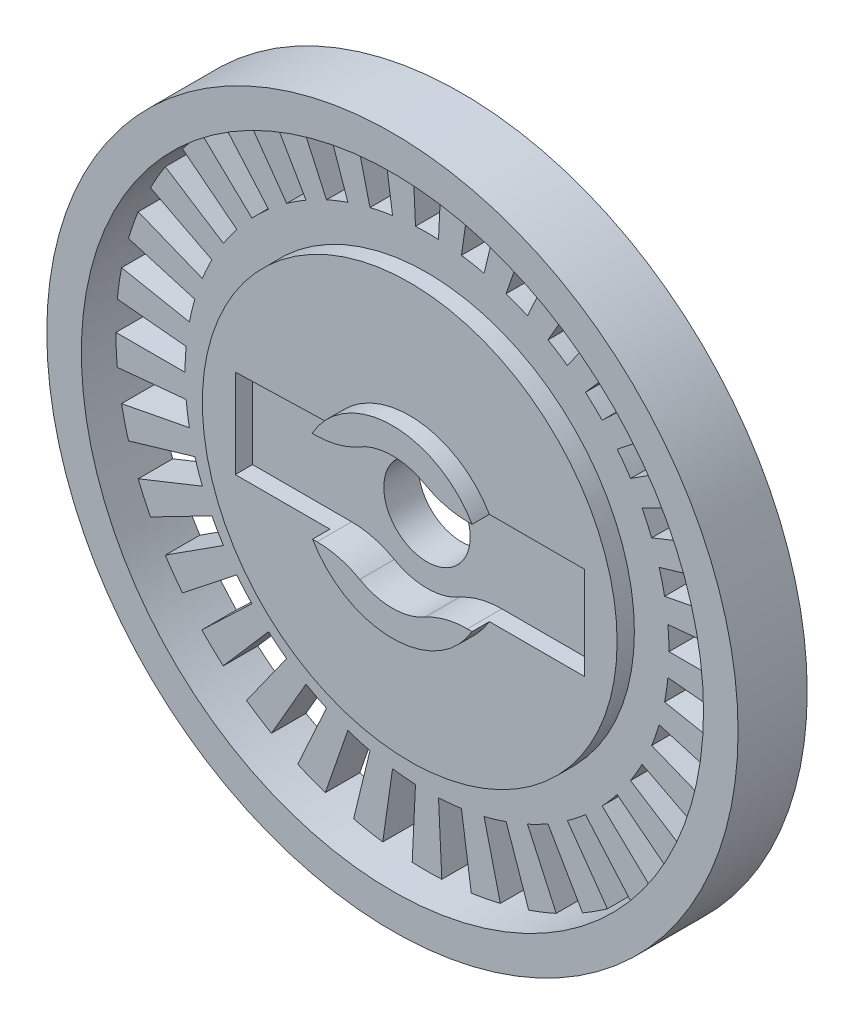
SolidWorks part; units mm, degrees
material "ABS"
ref_plane "Front Plane" through (0, 0, 0) normal (0, 0, 1) x (1, 0, 0)
ref_plane "Top Plane" through (0, 0, 0) normal (0, 1, 0) x (1, 0, 0)
ref_plane "Right Plane" through (0, 0, 0) normal (1, 0, 0) x (0, 0, -1)
sketch "Sketch1" plane through (0, 0, 0) normal (0, 0, 1) x (1, 0, 0)
  circle A0 centre (0, 0) radius 20
  dimension "D1" = 40
extrude "Boss-Extrude1" add sketch "Sketch1" along normal blind 4
sketch "Sketch2" plane through (0, 0, 4) normal (0, 0, 1) x (1, 0, 0)
  circle A0 centre (0, 0) radius 2.5
  dimension "D1" = 5
extrude "Cut-Extrude1" cut sketch "Sketch2" against normal blind 4
sketch "Sketch3" plane through (0, 0, 4) normal (0, 0, 1) x (1, 0, 0)
  line L6 (0, 0) -> (10.109, 0.0032) construction
  line L13 (10.075, 1.7016) -> (2.716, 2.6933) construction
  line L14 (10, 1.6361) -> (2.6806, 2.6224) construction
  line L15 (2.7051, -2.5972) -> (10, -5.8129) construction
  line L16 (2.7225, -2.6868) -> (10.075, -5.9279) construction
  line L17 (10.075, -5.9279) -> (10.075, 1.7016) construction
  line L18 (10, -5.8129) -> (10, 1.6361) construction
  line L19 (-10.075, 2.1965) -> (-2.9216, 2.4688) construction
  line L20 (-10, 2.1243) -> (-2.8855, 2.3951) construction
  line L21 (-2.7034, -2.5989) -> (-10, -1.9654) construction
  line L22 (-2.7378, -2.6712) -> (-10.075, -2.0342) construction
  line L23 (-10.075, -2.0342) -> (-10.075, 2.1965) construction
  line L24 (-10, -1.9654) -> (-10, 2.1243) construction
  line L25 (-2.7378, -2.6712) -> (-10.0936, -2.6712)
  line L26 (-10.0936, -2.6712) -> (-10.0936, 2.4688)
  line L29 (10.109, 0.0032) -> (10.109, -2.6868)
  line L30 (10.109, -2.6868) -> (2.7225, -2.6868)
  line L31 (2.7207, 2.6885) -> (10.109, 2.6885)
  line L32 (-2.7395, 2.6694) -> (-10.0936, 2.4688)
  line L33 (10.109, 2.6885) -> (10.109, 0.0032)
  arc A0 (-2.7034, -2.5989) -> (2.7051, -2.5972) centre (0, 0) ccw construction
  arc A1 (-2.7395, 2.6694) -> (2.7207, 2.6885) centre (0, 0) cw
  arc A4 (-2.7378, -2.6712) -> (2.7225, -2.6868) centre (0, 0) ccw
  arc A5 (2.6806, 2.6224) -> (-2.8855, 2.3951) centre (0, 0) ccw construction
  arc A6 (2.716, 2.6933) -> (-2.9216, 2.4688) centre (0, 0) ccw construction
  dimension "D1" = 5.4603
  dimension "D3" = 0.075
extrude "Cut-Extrude2" cut sketch "Sketch3" against normal blind 2
sketch "Sketch4" plane through (0, 0, 4) normal (0, 0, 1) x (1, 0, 0)
  line L0 (0, 0) -> (15, 0) construction
  line L1 (0, 0) -> (14.9321, 1.4258) construction
  line L2 (13.9366, 1.3308) -> (17.9185, 1.711)
  line L3 (14, 0) -> (18, 0)
  line L4 (-20, 0) -> (20, 0) construction
  line L5 (13.9366, -1.3308) -> (17.9185, -1.711)
  line L6 (13.747, -2.6495) -> (17.6747, -3.4065)
  line L7 (13.4329, -3.9443) -> (17.2709, -5.0712)
  line L8 (12.9972, -5.2033) -> (16.7106, -6.6899)
  line L9 (12.4437, -6.4152) -> (15.999, -8.2481)
  line L10 (11.7775, -7.569) -> (15.1426, -9.7315)
  line L11 (11.0047, -8.6542) -> (14.149, -11.1269)
  line L12 (10.1323, -9.6611) -> (13.0272, -12.4214)
  line L13 (9.1681, -10.5805) -> (11.7875, -13.6035)
  line L14 (8.1208, -11.4041) -> (10.441, -14.6624)
  line L15 (7, -12.1244) -> (9, -15.5885)
  line L16 (5.8158, -12.7348) -> (7.4775, -16.3734)
  line L17 (4.579, -13.23) -> (5.8872, -17.01)
  line L18 (3.3006, -13.6054) -> (4.2437, -17.4926)
  line L19 (1.9924, -13.8575) -> (2.5617, -17.8168)
  line L20 (0.6661, -13.9841) -> (0.8565, -17.9796)
  line L21 (-0.6661, -13.9841) -> (-0.8565, -17.9796)
  line L22 (-1.9924, -13.8575) -> (-2.5617, -17.8168)
  line L23 (-3.3006, -13.6054) -> (-4.2437, -17.4926)
  line L24 (-4.579, -13.23) -> (-5.8872, -17.01)
  line L25 (-5.8158, -12.7348) -> (-7.4775, -16.3734)
  line L26 (-7, -12.1244) -> (-9, -15.5885)
  line L27 (-8.1208, -11.4041) -> (-10.441, -14.6624)
  line L28 (-9.1681, -10.5805) -> (-11.7875, -13.6035)
  line L29 (-10.1323, -9.6611) -> (-13.0272, -12.4214)
  line L30 (-11.0047, -8.6542) -> (-14.149, -11.1269)
  line L31 (-11.7775, -7.569) -> (-15.1426, -9.7315)
  line L32 (-12.4437, -6.4152) -> (-15.999, -8.2481)
  line L33 (-12.9972, -5.2033) -> (-16.7106, -6.6899)
  line L34 (-13.4329, -3.9443) -> (-17.2709, -5.0712)
  line L35 (-13.747, -2.6495) -> (-17.6747, -3.4065)
  line L36 (-13.9366, -1.3308) -> (-17.9185, -1.711)
  line L37 (-14, 0) -> (-18, 0)
  line L38 (-13.9366, 1.3308) -> (-17.9185, 1.711)
  line L39 (-13.747, 2.6495) -> (-17.6747, 3.4065)
  line L40 (-13.4329, 3.9443) -> (-17.2709, 5.0712)
  line L41 (-12.9972, 5.2033) -> (-16.7106, 6.6899)
  line L42 (-12.4437, 6.4152) -> (-15.999, 8.2481)
  line L43 (-11.7775, 7.569) -> (-15.1426, 9.7315)
  line L44 (-11.0047, 8.6542) -> (-14.149, 11.1269)
  line L45 (-10.1323, 9.6611) -> (-13.0272, 12.4214)
  line L46 (-9.1681, 10.5805) -> (-11.7875, 13.6035)
  line L47 (-8.1208, 11.4041) -> (-10.441, 14.6624)
  line L48 (-7, 12.1244) -> (-9, 15.5885)
  line L49 (-5.8158, 12.7348) -> (-7.4775, 16.3734)
  line L50 (-4.579, 13.23) -> (-5.8872, 17.01)
  line L51 (-3.3006, 13.6054) -> (-4.2437, 17.4926)
  line L52 (-1.9924, 13.8575) -> (-2.5617, 17.8168)
  line L53 (-0.6661, 13.9841) -> (-0.8565, 17.9796)
  line L54 (0.6661, 13.9841) -> (0.8565, 17.9796)
  line L55 (1.9924, 13.8575) -> (2.5617, 17.8168)
  line L56 (3.3006, 13.6054) -> (4.2437, 17.4926)
  line L57 (4.579, 13.23) -> (5.8872, 17.01)
  line L58 (5.8158, 12.7348) -> (7.4775, 16.3734)
  line L59 (7, 12.1244) -> (9, 15.5885)
  line L60 (8.1208, 11.4041) -> (10.441, 14.6624)
  line L61 (9.1681, 10.5805) -> (11.7875, 13.6035)
  line L62 (10.1323, 9.6611) -> (13.0272, 12.4214)
  line L63 (11.0047, 8.6542) -> (14.149, 11.1269)
  line L64 (11.7775, 7.569) -> (15.1426, 9.7315)
  line L65 (12.4437, 6.4152) -> (15.999, 8.2481)
  line L66 (12.9972, 5.2033) -> (16.7106, 6.6899)
  line L67 (13.4329, 3.9443) -> (17.2709, 5.0712)
  line L68 (13.747, 2.6495) -> (17.6747, 3.4065)
  line L69 (0, 0) -> (19.3185, -5.1764) construction
  line L70 (0, 0) -> (-19.3185, -5.1764) construction
  circle A0 centre (0, 0) radius 15 construction
  arc A1 (14, 0) -> (13.9366, 1.3308) centre (0, 0) ccw construction
  arc A2 (18, 0) -> (17.9185, 1.711) centre (0, 0) ccw
  arc A3 (13.9366, 1.3308) -> (14, 0) centre (0, 0) cw
  circle A4 centre (0, 0) radius 20 construction
  arc A5 (17.6747, -3.4065) -> (17.9185, -1.711) centre (0, 0) ccw
  arc A6 (13.9366, -1.3308) -> (13.747, -2.6495) centre (0, 0) cw
  arc A7 (16.7106, -6.6899) -> (17.2709, -5.0712) centre (0, 0) ccw
  arc A8 (13.4329, -3.9443) -> (12.9972, -5.2033) centre (0, 0) cw
  arc A9 (15.1426, -9.7315) -> (15.999, -8.2481) centre (0, 0) ccw
  arc A10 (12.4437, -6.4152) -> (11.7775, -7.569) centre (0, 0) cw
  arc A11 (13.0272, -12.4214) -> (14.149, -11.1269) centre (0, 0) ccw
  arc A12 (11.0047, -8.6542) -> (10.1323, -9.6611) centre (0, 0) cw
  arc A13 (10.441, -14.6624) -> (11.7875, -13.6035) centre (0, 0) ccw
  arc A14 (9.1681, -10.5805) -> (8.1208, -11.4041) centre (0, 0) cw
  arc A15 (7.4775, -16.3734) -> (9, -15.5885) centre (0, 0) ccw
  arc A16 (7, -12.1244) -> (5.8158, -12.7348) centre (0, 0) cw
  arc A17 (4.2437, -17.4926) -> (5.8872, -17.01) centre (0, 0) ccw
  arc A18 (4.579, -13.23) -> (3.3006, -13.6054) centre (0, 0) cw
  arc A19 (0.8565, -17.9796) -> (2.5617, -17.8168) centre (0, 0) ccw
  arc A20 (1.9924, -13.8575) -> (0.6661, -13.9841) centre (0, 0) cw
  arc A21 (-2.5617, -17.8168) -> (-0.8565, -17.9796) centre (0, 0) ccw
  arc A22 (-0.6661, -13.9841) -> (-1.9924, -13.8575) centre (0, 0) cw
  arc A23 (-5.8872, -17.01) -> (-4.2437, -17.4926) centre (0, 0) ccw
  arc A24 (-3.3006, -13.6054) -> (-4.579, -13.23) centre (0, 0) cw
  arc A25 (-9, -15.5885) -> (-7.4775, -16.3734) centre (0, 0) ccw
  arc A26 (-5.8158, -12.7348) -> (-7, -12.1244) centre (0, 0) cw
  arc A27 (-11.7875, -13.6035) -> (-10.441, -14.6624) centre (0, 0) ccw
  arc A28 (-8.1208, -11.4041) -> (-9.1681, -10.5805) centre (0, 0) cw
  arc A29 (-14.149, -11.1269) -> (-13.0272, -12.4214) centre (0, 0) ccw
  arc A30 (-10.1323, -9.6611) -> (-11.0047, -8.6542) centre (0, 0) cw
  arc A31 (-15.999, -8.2481) -> (-15.1426, -9.7315) centre (0, 0) ccw
  arc A32 (-11.7775, -7.569) -> (-12.4437, -6.4152) centre (0, 0) cw
  arc A33 (-17.2709, -5.0712) -> (-16.7106, -6.6899) centre (0, 0) ccw
  arc A34 (-12.9972, -5.2033) -> (-13.4329, -3.9443) centre (0, 0) cw
  arc A35 (-17.9185, -1.711) -> (-17.6747, -3.4065) centre (0, 0) ccw
  arc A36 (-13.747, -2.6495) -> (-13.9366, -1.3308) centre (0, 0) cw
  arc A37 (-17.9185, 1.711) -> (-18, 0) centre (0, 0) ccw
  arc A38 (-14, 0) -> (-13.9366, 1.3308) centre (0, 0) cw
  arc A39 (-17.2709, 5.0712) -> (-17.6747, 3.4065) centre (0, 0) ccw
  arc A40 (-13.747, 2.6495) -> (-13.4329, 3.9443) centre (0, 0) cw
  arc A41 (-15.999, 8.2481) -> (-16.7106, 6.6899) centre (0, 0) ccw
  arc A42 (-12.9972, 5.2033) -> (-12.4437, 6.4152) centre (0, 0) cw
  arc A43 (-14.149, 11.1269) -> (-15.1426, 9.7315) centre (0, 0) ccw
  arc A44 (-11.7775, 7.569) -> (-11.0047, 8.6542) centre (0, 0) cw
  arc A45 (-11.7875, 13.6035) -> (-13.0272, 12.4214) centre (0, 0) ccw
  arc A46 (-10.1323, 9.6611) -> (-9.1681, 10.5805) centre (0, 0) cw
  arc A47 (-9, 15.5885) -> (-10.441, 14.6624) centre (0, 0) ccw
  arc A48 (-8.1208, 11.4041) -> (-7, 12.1244) centre (0, 0) cw
  arc A49 (-5.8872, 17.01) -> (-7.4775, 16.3734) centre (0, 0) ccw
  arc A50 (-5.8158, 12.7348) -> (-4.579, 13.23) centre (0, 0) cw
  arc A51 (-2.5617, 17.8168) -> (-4.2437, 17.4926) centre (0, 0) ccw
  arc A52 (-3.3006, 13.6054) -> (-1.9924, 13.8575) centre (0, 0) cw
  arc A53 (0.8565, 17.9796) -> (-0.8565, 17.9796) centre (0, 0) ccw
  arc A54 (-0.6661, 13.9841) -> (0.6661, 13.9841) centre (0, 0) cw
  arc A55 (4.2437, 17.4926) -> (2.5617, 17.8168) centre (0, 0) ccw
  arc A56 (1.9924, 13.8575) -> (3.3006, 13.6054) centre (0, 0) cw
  arc A57 (7.4775, 16.3734) -> (5.8872, 17.01) centre (0, 0) ccw
  arc A58 (4.579, 13.23) -> (5.8158, 12.7348) centre (0, 0) cw
  arc A59 (10.441, 14.6624) -> (9, 15.5885) centre (0, 0) ccw
  arc A60 (7, 12.1244) -> (8.1208, 11.4041) centre (0, 0) cw
  arc A61 (13.0272, 12.4214) -> (11.7875, 13.6035) centre (0, 0) ccw
  arc A62 (9.1681, 10.5805) -> (10.1323, 9.6611) centre (0, 0) cw
  arc A63 (15.1426, 9.7315) -> (14.149, 11.1269) centre (0, 0) ccw
  arc A64 (11.0047, 8.6542) -> (11.7775, 7.569) centre (0, 0) cw
  arc A65 (16.7106, 6.6899) -> (15.999, 8.2481) centre (0, 0) ccw
  arc A66 (12.4437, 6.4152) -> (12.9972, 5.2033) centre (0, 0) cw
  arc A67 (17.6747, 3.4065) -> (17.2709, 5.0712) centre (0, 0) ccw
  arc A68 (13.4329, 3.9443) -> (13.747, 2.6495) centre (0, 0) cw
  point P15 (0, 0)
  point P114 (0, 0)
  point P146 (0, 0)
  dimension "D1" = 5.455
  dimension "D3" = 14
  dimension "D5" = 15
  dimension "D6" = 15
  dimension "D2" = 4
  dimension "D4" = 33
extrude "Cut-Extrude3" cut sketch "Sketch4" against normal blind 4
sketch "Sketch5" plane through (0, 0, 4) normal (0, 0, 1) x (1, 0, 0)
  circle A0 centre (0, 0) radius 12
  circle A2 centre (0, 0) radius 18
  arc A4 (14, 0) -> (13.9366, 1.3308) centre (0, 0) ccw construction
  dimension "D1" = 2
  dimension "D2" = 6
extrude "Cut-Extrude4" cut sketch "Sketch5" against normal blind 2
sketch "Sketch6" plane through (0, 0, 4) normal (0, 0, 1) x (1, 0, 0)
  circle A0 centre (0, 0) radius 13.3357
  circle A1 centre (0, 0) radius 5.3357
  dimension "D1" = 8
extrude "Cut-Extrude5" cut sketch "Sketch6" against normal blind 1
fillet "Fillet2" radius 5 4 edges at (-2.7395, 2.6694, 3) (2.7207, 2.6885, 3) (2.7225, -2.6868, 3) (-2.7378, -2.6712, 3)
